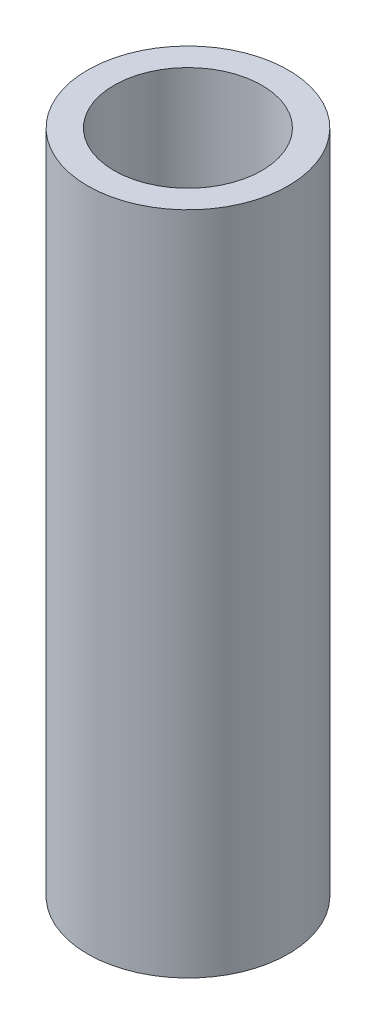
SolidWorks part; units mm, degrees
ref_plane "Front Plane" through (0, 0, 0) normal (0, 0, 1) x (1, 0, 0)
ref_plane "Top Plane" through (0, 0, 0) normal (0, 1, 0) x (1, 0, 0)
ref_plane "Right Plane" through (0, 0, 0) normal (1, 0, 0) x (0, 0, -1)
sketch "Sketch1" plane through (0, 0, 0) normal (0, 1, 0) x (1, 0, 0)
  circle A0 centre (0, 0) radius 0.889
  circle A1 centre (0, 0) radius 1.2065
  dimension "D1" = 1.778
  dimension "D2" = 2.413
extrude "Boss-Extrude1" add sketch "Sketch1" along normal blind 6 and the other way blind 2
